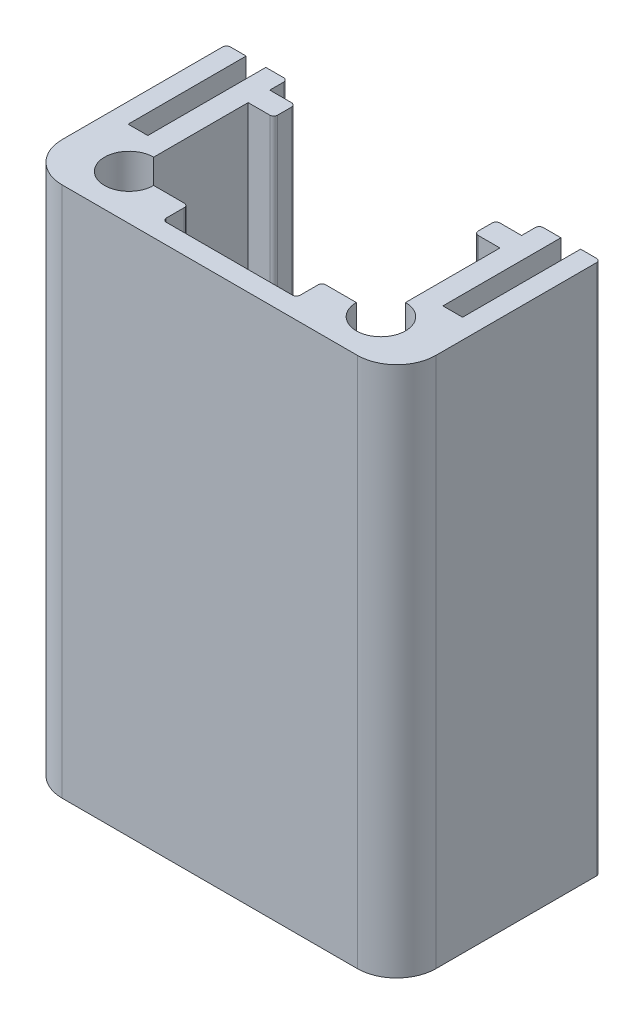
SolidWorks part; units mm, degrees
ref_plane "前视基准面" through (0, 0, 0) normal (0, 0, 1) x (1, 0, 0)
ref_plane "上视基准面" through (0, 0, 0) normal (0, 1, 0) x (1, 0, 0)
ref_plane "右视基准面" through (0, 0, 0) normal (1, 0, 0) x (0, 0, -1)
sketch "草图1" plane through (0, 0, 0) normal (0, 1, 0) x (1, 0, 0)
  line L0 (-57.4345, 0) -> (51.691, 0) construction
  line L1 (0, 59.2926) -> (0, -60.9819) construction
  line L2 (-9.5, 11.35) -> (-9.5, 0)
  line L3 (-9.5, 0) -> (9.5, 0)
  line L4 (9.5, 0) -> (9.5, 11.35)
  line L5 (9.5, 11.35) -> (5.1, 11.35)
  line L6 (-6.4, 8.35) -> (-6.4, 2.3)
  line L7 (-6.4, 2.3) -> (6.4, 2.3)
  line L8 (6.4, 2.3) -> (6.4, 8.35)
  line L9 (6.4, 8.35) -> (5.1, 8.35)
  line L10 (5.1, 8.35) -> (5.1, 11.35)
  line L11 (-6.4, 8.35) -> (-5.1, 8.35)
  line L12 (-5.1, 8.35) -> (-5.1, 11.35)
  line L13 (-5.1, 11.35) -> (-9.5, 11.35)
  dimension "D1" = 19
  dimension "D2" = 12.8
  dimension "D3" = 1.3
  dimension "D4" = 2.3
  dimension "D5" = 6.05
  dimension "D6" = 3
extrude "凸台-拉伸1" add sketch "草图1" along normal blind 27
sketch "草图3" plane through (0, 27, 0) normal (0, 1, 0) x (1, 0, 0)
  line L0 (-8.5, 11.35) -> (-7.5, 11.35)
  line L1 (-5.1, 11.35) -> (-9.5, 11.35) construction
  line L2 (-7.5, 11.35) -> (-7.5, 4.35)
  line L3 (-7.5, 4.35) -> (-8.5, 4.35)
  line L4 (-8.5, 4.35) -> (-8.5, 11.35)
  line L5 (-9.5, 11.35) -> (-9.5, 0) construction
  line L7 (0, 11.5268) -> (0, -2.7437) construction
  line L8 (8.5, 4.35) -> (8.5, 11.35)
  line L9 (7.5, 4.35) -> (8.5, 4.35)
  line L10 (7.5, 11.35) -> (7.5, 4.35)
  line L11 (8.5, 11.35) -> (7.5, 11.35)
  dimension "D1" = 1
  dimension "D2" = 1
  dimension "D3" = 7
extrude "切除-拉伸1" cut sketch "草图3" against normal up to next
sketch "草图8" plane through (0, 0, -11.35) normal (0, 0, -1) x (-1, 0, 0)
  line L0 (6.4, 27) -> (-6.4, 27)
  line L1 (5.1, 27) -> (7.5, 27) construction
  line L3 (-6.4, 27) -> (-6.4, 0)
  line L4 (-6.4, 0) -> (6.4, 0)
  line L5 (6.4, 0) -> (6.4, 27)
  line L6 (7.5, 0) -> (7.5, 27) construction
  line L8 (-9.5, 0) -> (-8.5, 0) construction
  line L9 (-7.5, 0) -> (-7.5, 27) construction
  line L10 (-7.5, 27) -> (-5.1, 27) construction
  dimension "D1" = 1.1
  dimension "D2" = 1.1
extrude "切除-拉伸4" cut sketch "草图8" against normal blind 1.9
sketch "草图9" plane through (0, 0, 0) normal (0, -1, 0) x (1, 0, 0)
  line L0 (0, -11.9945) -> (0, 8.1962) construction
  line L1 (3.4, -2.3) -> (3.4, -1)
  line L2 (6.4, -2.3) -> (-6.4, -2.3) construction
  line L3 (3.4, -1) -> (-3.4, -1)
  line L4 (-3.4, -1) -> (-3.4, -2.3)
  line L5 (-3.4, -2.3) -> (3.4, -2.3)
  line L6 (6.4, -8.35) -> (6.4, -2.3) construction
  line L7 (-9.5, 0) -> (9.5, 0) construction
  circle A0 centre (-6.4, -2.3) radius 1.15
  circle A1 centre (6.4, -2.3) radius 1.15
  dimension "D1" = 2.3
  dimension "D2" = 3
  dimension "D3" = 1
extrude "切除-拉伸5" cut sketch "草图9" against normal up to next
sketch "草图11" plane through (0, 27, 0) normal (0, 1, 0) x (1, 0, 0)
  line L0 (6.4, 11.35) -> (9.5, 11.35)
  line L1 (9.5, 11.35) -> (9.5, 10.35)
  line L2 (9.5, 0) -> (9.5, 11.35) construction
  line L3 (9.5, 10.35) -> (6.4, 10.35)
  line L5 (6.4, 10.35) -> (6.4, 11.35)
  line L6 (-9.5, 11.35) -> (-6.4, 11.35)
  line L7 (-6.4, 11.35) -> (-6.4, 10.35)
  line L9 (-6.4, 10.35) -> (-9.5, 10.35)
  line L10 (-9.5, 11.35) -> (-9.5, 0) construction
  line L11 (-9.5, 10.35) -> (-9.5, 11.35)
  line L12 (-6.4, 9.45) -> (-6.4, 11.35) construction
  line L13 (6.4, 9.45) -> (6.4, 11.35) construction
  dimension "D1" = 1
extrude "切除-拉伸6" cut sketch "草图11" against normal up to next
chamfer "倒角1" [suppressed] distance 0.5 angle 45
fillet "圆角1" radius 2 2 edges at (-9.5, 13.5, 0) (9.5, 13.5, 0)
fillet "圆角2" radius 0.2 12 edges at (3.4, 13.5, -2.3) (3.4, 13.5, -1) (-3.4, 13.5, -1) (-3.4, 13.5, -2.3) (5.1, 13.5, -8.35) (-5.1, 13.5, -8.35) (5.1, 13.5, -9.45) (-5.1, 13.5, -9.45) (-6.4, 13.5, -10.35) (6.4, 13.5, -10.35) (9.5, 13.5, -10.35) (-9.5, 13.5, -10.35)
hole_wizard "M3 螺纹孔1" positions "草图12" profile "草图13" tap size "M3" standard "GB"
sketch "草图12" plane through (0, 27, 0) normal (0, 1, 0) x (1, 0, 0)
  point P0 (-6.4, 2.3)
  point P3 (6.4, 2.3)
sketch "草图13" plane through (-6.4, 27, -2.3) normal (1, 0, 0) x (0, 0, 1)
  line L0 (0, 0) -> (0, 9.2511)
  line L1 (0, 9.2511) -> (1.25, 8.5)
  line L2 (1.25, 8.5) -> (1.25, 0)
  line L5 (1.25, 0) -> (0, 0)
  line L10 (0, 9.2511) -> (-1.25, 8.5) construction
  line L11 (0, -6.35) -> (0, 107.95) construction
  dimension "螺纹孔钻头直径" = 2.5
  dimension "螺纹孔钻头深度" = 8.5
  dimension "导头角度" = 118
cosmetic thread "孔螺蚊线1" parameters "D1"=6, "D2"=3
cosmetic thread "孔螺蚊线2" parameters "D1"=6, "D2"=3
